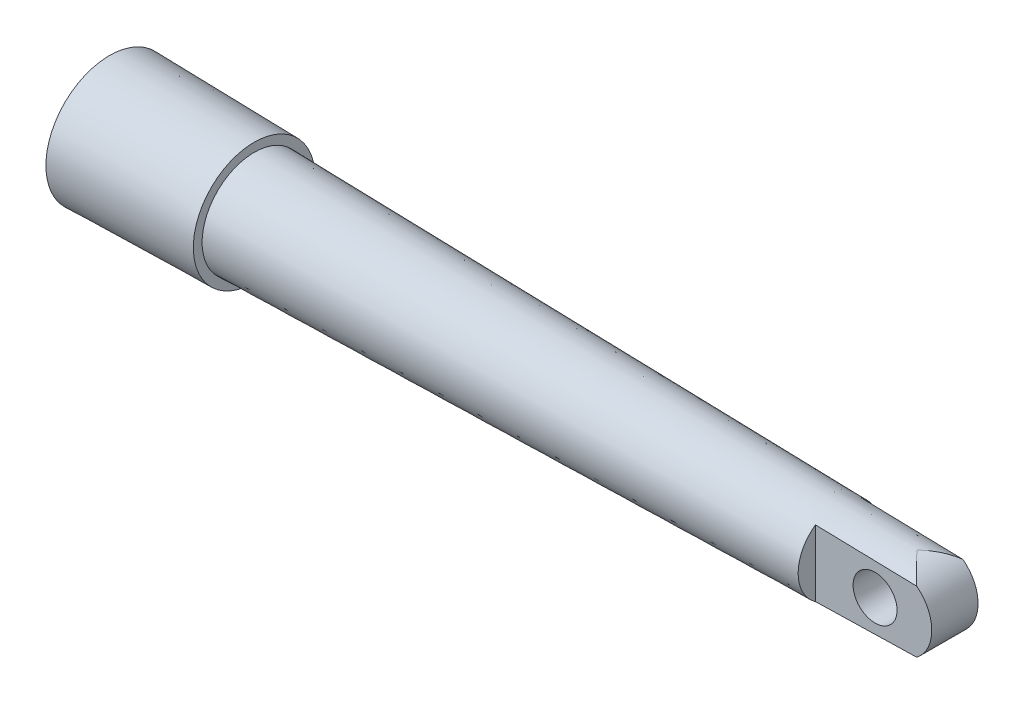
SolidWorks part; units mm, degrees
ref_plane "Front Plane" through (0, 0, 0) normal (0, 0, 1) x (1, 0, 0)
ref_plane "Top Plane" through (0, 0, 0) normal (0, 1, 0) x (1, 0, 0)
ref_plane "Right Plane" through (0, 0, 0) normal (1, 0, 0) x (0, 0, -1)
sketch "Sketch1" plane through (0, 0, 0) normal (0, 0, 1) x (1, 0, 0)
  line L0 (157.5, 0) -> (0, 0)
  line L1 (0, 0) -> (0, 13.75)
  line L2 (0, 13.75) -> (31.25, 13.15)
  line L3 (31.25, 13.15) -> (31.25, 11.25)
  line L4 (31.25, 11.25) -> (157.5, 8.75)
  line L5 (157.5, 8.75) -> (157.5, 0)
  line L6 (157.5, 0) -> (153.3868, 0) construction
  dimension "D1" = 13.75
  dimension "D2" = 13.15
  dimension "D3" = 31.25
  dimension "D4" = 8.75
  dimension "D5" = 157.5
  dimension "D6" = 11.25
ref_plane "Plane2" through (0, 0, 0) normal (0, 0, 1) x (1, 0, 0)
revolve "Revolve2" add sketch "Sketch1" angle 360 about L6
ref_plane "Plane4" through (0, 0, 0) normal (0, 0, 1) x (1, 0, 0)
sketch "Sketch2" plane through (0, 0, 0) normal (0, 0, 1) x (1, 0, 0)
  line L0 (157.5, 0) -> (181.25, 0) construction
  line L1 (157.5, -8.75) -> (157.5, 8.75) construction
  line L2 (157.5, 8.75) -> (174.2967, 8.4174)
  line L3 (157.5, -8.75) -> (174.2967, -8.4174)
  line L4 (157.5, 8.75) -> (157.5, -8.75)
  line L5 (157.5, 8.75) -> (31.25, 11.25) construction
  arc A0 (174.2967, 8.4174) -> (174.2967, -8.4174) centre (174.2004, 0) cw
  dimension "D1" = 23.75
  dimension "D2" = 16.8
extrude "Boss-Extrude2" add sketch "Sketch2" along normal mid plane 10
sketch "Sketch6" plane through (0, 0, 0) normal (0, 0, 1) x (1, 0, 0)
  line L0 (157.5, 8.75) -> (157.5, 12.5)
  line L1 (157.5, 12.5) -> (189.266, 12.5)
  line L2 (189.266, 8.121) -> (189.266, 12.5)
  line L3 (157.5, 8.75) -> (189.266, 8.121)
  line L5 (174.2967, 8.4174) -> (157.5, 8.75) construction
  line L6 (157.5, 0) -> (194.0296, 0) construction
  line L7 (157.5, 7.1807) -> (157.5, -7.1807) construction
  dimension "D1" = 12.5
revolve "Cut-Revolve1" cut sketch "Sketch6" angle 360 about L6
sketch "Sketch7" plane through (0, 0, 5) normal (0, 0, 1) x (1, 0, 0)
  line L0 (157.5, 0) -> (172.8353, 0) construction
  line L1 (157.5, 7.1807) -> (157.5, -7.1807) construction
  line L2 (172.8353, 0) -> (175.1184, 0)
  circle A0 centre (170.3684, 0) radius 4.75
  arc A3 (179.3666, -6.6462) -> (179.3666, 6.6462) centre (174.2004, 0) ccw construction
  point P10 (182.6184, 0)
  dimension "D1" = 9.5
  dimension "D2" = 7.5
extrude "Cut-Extrude1" cut sketch "Sketch7" against normal through all contours L0 A0 L2 | A0 L0 L2
sketch "Sketch8" plane through (0, 0, 0) normal (-1, 0, 0) x (0, 0, 1)
  circle A0 centre (0, 0) radius 5
  dimension "D1" = 10
extrude "Cut-Extrude2" cut sketch "Sketch8" against normal blind 132.5
